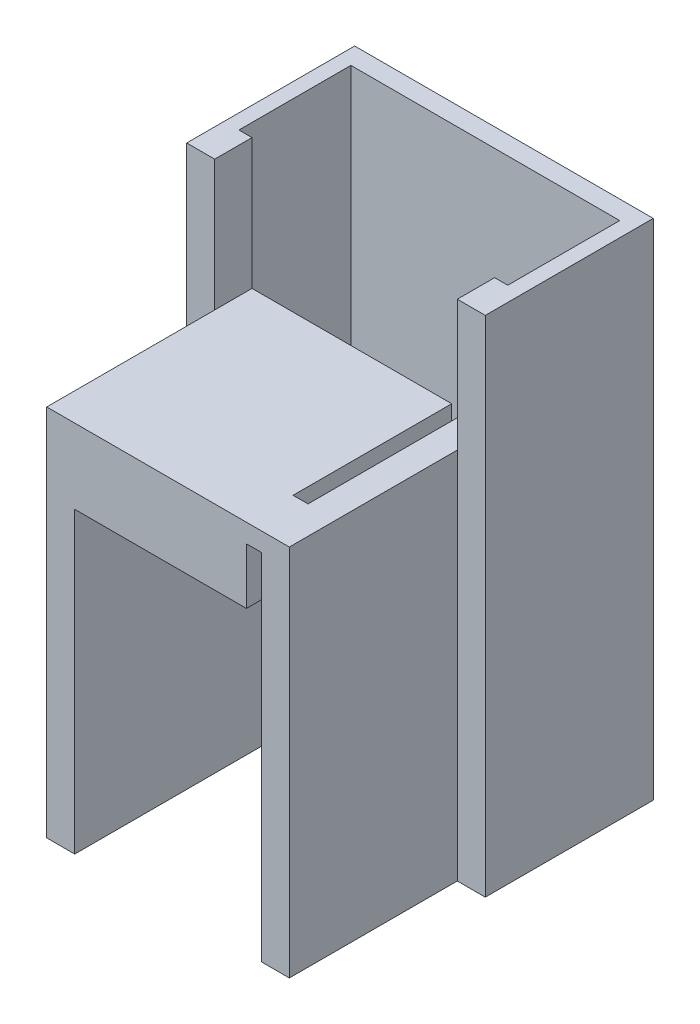
SolidWorks part; units mm, degrees
ref_plane "Front Plane" through (0, 0, 0) normal (0, 0, 1) x (1, 0, 0)
ref_plane "Top Plane" through (0, 0, 0) normal (0, 1, 0) x (1, 0, 0)
ref_plane "Right Plane" through (0, 0, 0) normal (1, 0, 0) x (0, 0, -1)
sketch "Sketch1" plane through (0, 0, 0) normal (0, 0, 1) x (1, 0, 0)
  line L0 (0, 0) -> (0, 20.32)
  line L1 (0, 20.32) -> (-12.7, 20.32)
  line L2 (-12.7, 20.32) -> (-12.7, 0)
  line L3 (-12.7, 0) -> (-14.605, 0)
  line L4 (-14.605, 0) -> (-14.605, 25.4)
  line L6 (-14.605, 25.4) -> (1.905, 25.4)
  line L8 (1.905, 25.4) -> (1.905, 0)
  line L9 (1.905, 0) -> (0, 0)
extrude "Boss-Extrude1" add sketch "Sketch1" against normal blind 13.97
sketch "Sketch3" plane through (0, 0, 0) normal (0, 0, 1) x (1, 0, 0)
  line L0 (0, 20.32) -> (0, 24.13)
  line L1 (-12.7, 20.32) -> (0, 20.32) construction
  line L2 (0, 24.13) -> (-1.016, 24.13)
  line L3 (0, 20.32) -> (-1.016, 20.32)
  line L4 (-1.016, 24.13) -> (-1.016, 20.32)
extrude "Cut-Extrude1" cut sketch "Sketch3" against normal through all
sketch "Sketch4" plane through (0, 24.13, 0) normal (0, -1, 0) x (1, 0, 0)
  line L0 (-1.016, -6.985) -> (-1.016, -3.175)
  line L1 (-1.016, -13.97) -> (-1.016, 0) construction
  line L2 (-1.016, -13.97) -> (-1.016, 0) construction
  line L3 (-1.016, -3.175) -> (0, -3.175)
  line L4 (0, -13.97) -> (0, 0) construction
  line L5 (0, -3.175) -> (0, -13.97)
  line L6 (0, -13.97) -> (-1.016, -13.97)
  line L7 (-1.016, -13.97) -> (-1.016, -6.985)
  line L8 (0, -13.97) -> (-1.016, -13.97) construction
extrude "Cut-Extrude2" cut sketch "Sketch4" against normal through all
sketch "Sketch11" plane through (0, 25.4, 0) normal (0, 1, 0) x (1, 0, 0)
  line L1 (-15.4972, 13.97) -> (-14.605, 13.97)
  line L2 (3.81, 11.43) -> (3.81, 22.86)
  line L3 (3.81, 22.86) -> (-16.51, 22.86)
  line L4 (-16.51, 22.86) -> (-16.51, 11.43)
  line L6 (-16.51, 11.43) -> (-14.605, 11.43)
  line L8 (2.7972, 13.97) -> (2.7972, 21.59)
  line L9 (2.7972, 21.59) -> (-15.4972, 21.59)
  line L10 (-15.4972, 21.59) -> (-15.4972, 13.97)
  line L12 (-14.605, 13.97) -> (-14.605, 0) construction
  line L13 (-14.605, 13.97) -> (-14.605, 11.43)
  line L14 (2.7972, 13.97) -> (1.905, 13.97)
  line L15 (1.905, 13.97) -> (1.905, 11.43)
  line L16 (1.905, 13.97) -> (1.905, 0) construction
  line L17 (1.905, 11.43) -> (3.81, 11.43)
extrude "Boss-Extrude3" add sketch "Sketch11" against normal up to surface (25.4 mm away) and the other way blind 8.89 up to face at (0.9525, 0, -6.985)
sketch "Sketch12" plane through (0, 0, 0) normal (0, -1, 0) x (1, 0, 0)
  line L0 (-15.4972, -13.97) -> (2.7972, -13.97)
  line L1 (2.7972, -13.97) -> (2.7972, -21.59)
  line L2 (2.7972, -21.59) -> (-15.4972, -21.59)
  line L3 (-15.4972, -21.59) -> (-15.4972, -13.97)
extrude "Boss-Extrude4" add sketch "Sketch12" against normal blind 1.27
